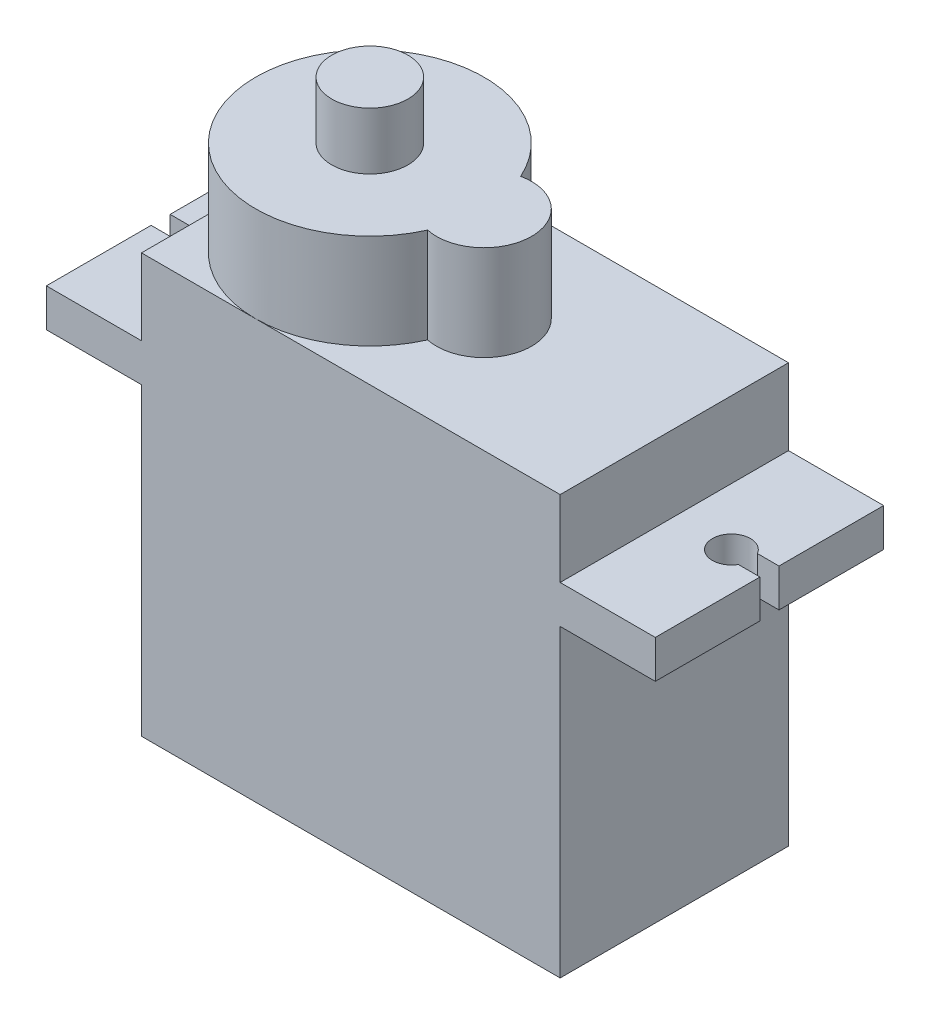
SolidWorks part; units mm, degrees
ref_plane "前视基准面" through (0, 0, 0) normal (0, 0, 1) x (1, 0, 0)
ref_plane "上视基准面" through (0, 0, 0) normal (0, 1, 0) x (1, 0, 0)
ref_plane "右视基准面" through (0, 0, 0) normal (1, 0, 0) x (0, 0, -1)
sketch "草图1" plane through (0, 0, 0) normal (0, 1, 0) x (1, 0, 0)
  line L1 (-11, -6) -> (11, -6)
  line L2 (-11, -6) -> (-11, 6)
  line L3 (-11, 6) -> (11, 6)
  line L4 (11, -6) -> (11, 6)
  line L5 (-11, -6) -> (11, 6) construction
  line L6 (-11, 6) -> (11, -6) construction
  point P0 (0, 0)
  dimension "D1" = 22
  dimension "D2" = 12
extrude "凸台-拉伸1" add sketch "草图1" along normal blind 22
sketch "草图3" plane through (0, 22, 0) normal (0, 1, 0) x (1, 0, 0)
  line L0 (-12.1, 0) -> (12.1, 0) construction
  line L1 (-11, 6) -> (-11, -6) construction
  line L2 (11, 6) -> (-11, 6) construction
  arc A0 (0.4792, 2.4451) -> (0.4792, -2.4451) centre (-5, 0) ccw
  arc A1 (0.4792, -2.4451) -> (0.4792, 2.4451) centre (1, 0) ccw
  dimension "D2" = 5
  dimension "D1" = 6
extrude "凸台-拉伸2" add sketch "草图3" along normal blind 5
sketch "草图4" plane through (0, 27, 0) normal (0, 1, 0) x (1, 0, 0)
  circle A0 centre (-5, 0) radius 2
  dimension "D1" = 4
extrude "凸台-拉伸3" add sketch "草图4" along normal blind 3
sketch "草图5" plane through (0, 0, 6) normal (0, 0, 1) x (1, 0, 0)
  line L0 (-11, 22) -> (-11, 0) construction
  line L1 (-16, 18) -> (-11, 18)
  line L2 (-16, 18) -> (-16, 16)
  line L3 (-16, 16) -> (-11, 16)
  line L4 (-11, 18) -> (-11, 16)
  line L5 (11, 22) -> (11, 0) construction
  line L6 (11, 18) -> (16, 18)
  line L7 (11, 18) -> (11, 16)
  line L8 (11, 16) -> (16, 16)
  line L9 (16, 18) -> (16, 16)
  line L10 (-11, 22) -> (-5, 22) construction
  line L11 (-5, 22) -> (11, 22) construction
  dimension "D1" = 2
  dimension "D2" = 4
  dimension "D3" = 5
  dimension "D4" = 5
  dimension "D5" = 2
  dimension "D6" = 4
extrude "凸台-拉伸4" add sketch "草图5" against normal up to surface (12 mm away) up to face at (-1, 13.2, -6)
sketch "草图6" plane through (-11, 0, 0) normal (-1, 0, 0) x (0, 0, 1)
  line L0 (6.6, 0) -> (-6.6, 0) construction
  line L1 (-1.5, 6.5) -> (1.5, 6.5)
  line L2 (-1.5, 6.5) -> (-1.5, 5)
  line L3 (-1.5, 5) -> (1.5, 5)
  line L4 (1.5, 6.5) -> (1.5, 5)
  line L5 (0, -16.5) -> (0, 16.5) construction
  dimension "D1" = 5
  dimension "D2" = 1.5
  dimension "D3" = 3
  dimension "D4" = 1.5
extrude "凸台-拉伸5" add sketch "草图6" along normal blind 3
sketch "草图7" plane through (0, 18, 0) normal (0, 1, 0) x (1, 0, 0)
  line L0 (-16.5, 0) -> (16.5, 0) construction
  line L1 (16, 6) -> (16, -6) construction
  line L2 (-16, 6) -> (-16, -6) construction
  line L4 (-16, -0.4956) -> (-14.8685, -0.4956)
  line L5 (-16, -0.4956) -> (-16, 0.5044)
  line L6 (-16, 0.5044) -> (-14.8635, 0.5044)
  line L8 (14.866, -0.5) -> (16, -0.5)
  line L10 (14.866, 0.5) -> (16, 0.5)
  line L11 (16, -0.5) -> (16, 0.5)
  arc A0 (-14.8685, -0.4956) -> (-14.8635, 0.5044) centre (-14, 0) ccw
  arc A1 (14.866, 0.5) -> (14.866, -0.5) centre (14, 0) ccw
  dimension "D1" = 2
  dimension "D2" = 2
  dimension "D5" = 1
  dimension "D3" = 2
  dimension "D4" = 2
  dimension "D6" = 0.5
  dimension "D7" = 1
  dimension "D8" = 0.4956
extrude "切除-拉伸1" cut sketch "草图7" against normal blind 3
